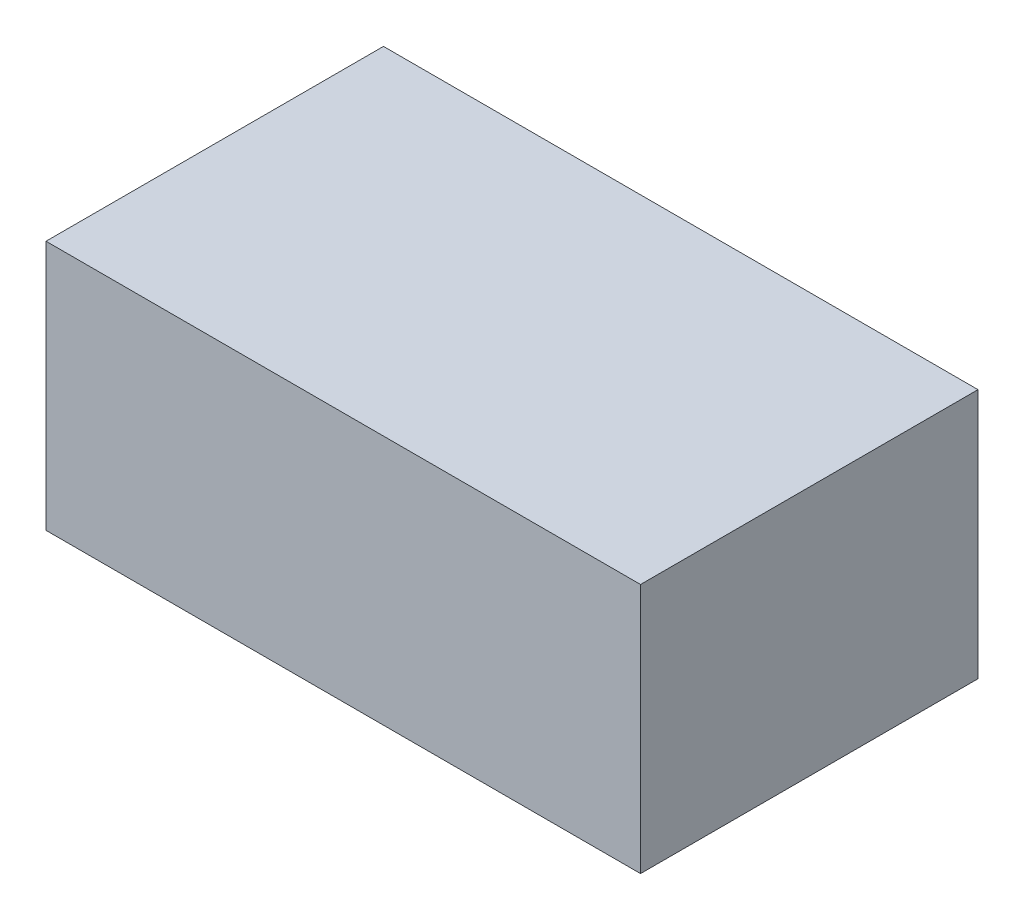
SolidWorks part; units mm, degrees
ref_plane "Front Plane" through (0, 0, 0) normal (0, 0, 1) x (1, 0, 0)
ref_plane "Top Plane" through (0, 0, 0) normal (0, 1, 0) x (1, 0, 0)
ref_plane "Right Plane" through (0, 0, 0) normal (1, 0, 0) x (0, 0, -1)
sketch "Sketch1" plane through (0, 0, 0) normal (0, 1, 0) x (1, 0, 0)
  line L1 (-83.1026, -47.1709) -> (83.1026, -47.1709)
  line L2 (-83.1026, -47.1709) -> (-83.1026, 47.1709)
  line L3 (-83.1026, 47.1709) -> (83.1026, 47.1709)
  line L4 (83.1026, -47.1709) -> (83.1026, 47.1709)
  line L5 (-83.1026, -47.1709) -> (83.1026, 47.1709) construction
  line L6 (-83.1026, 47.1709) -> (83.1026, -47.1709) construction
  point P0 (0, 0)
extrude "Boss-Extrude1" add sketch "Sketch1" along normal mid plane 70
